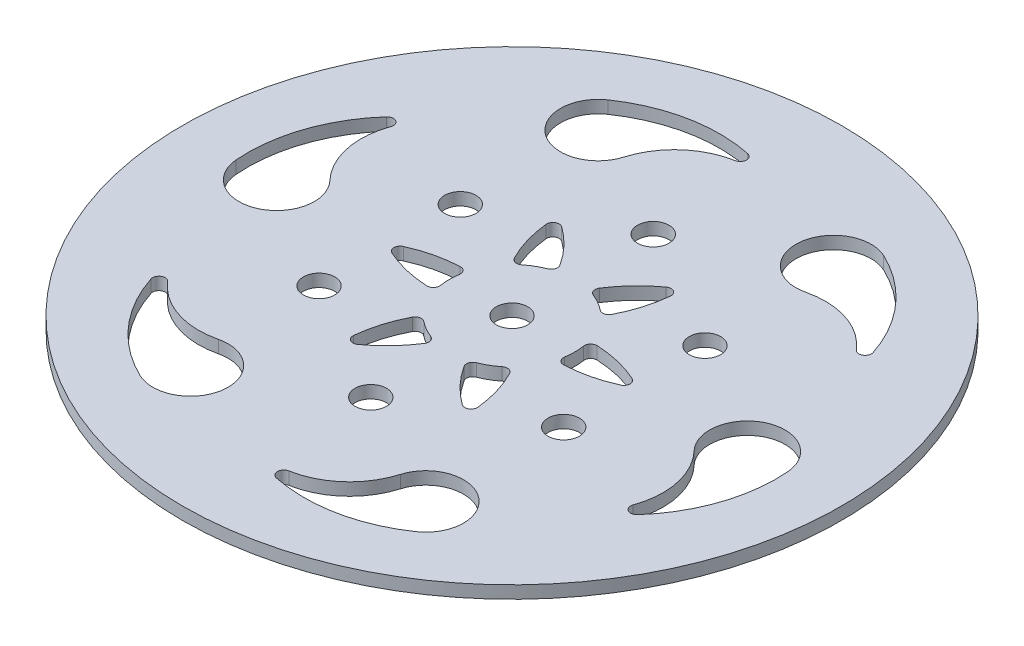
SolidWorks part; units mm, degrees
material "Thornel Mat VMA"
ref_plane "前视基准面" through (0, 0, 0) normal (0, 0, 1) x (1, 0, 0)
ref_plane "上视基准面" through (0, 0, 0) normal (0, 1, 0) x (1, 0, 0)
ref_plane "右视基准面" through (0, 0, 0) normal (1, 0, 0) x (0, 0, -1)
sketch "草图1" plane through (0, 0, 0) normal (0, 1, 0) x (1, 0, 0)
  circle A0 centre (0, 0) radius 52.5
  circle A2 centre (0, 0) radius 2.5
  point P19 (0, 0)
  point P33 (0, 0)
  dimension "D1" = 105
  dimension "D3" = 5
extrude "凸台-拉伸1" add sketch "草图1" along normal blind 2
sketch "草图2" plane through (0, 2, 0) normal (0, 1, 0) x (1, 0, 0)
  circle A0 centre (0, 0) radius 22.5 construction
  circle A1 centre (0, 22.5) radius 2.5
  circle A2 centre (19.4856, 11.25) radius 2.5
  circle A3 centre (19.4856, -11.25) radius 2.5
  circle A4 centre (0, -22.5) radius 2.5
  circle A5 centre (-19.4856, -11.25) radius 2.5
  circle A6 centre (-19.4856, 11.25) radius 2.5
  point P18 (0, 0)
  dimension "D1" = 45
  dimension "D2" = 5
  dimension "D3" = 6
extrude "切除-拉伸1" cut sketch "草图2" against normal through all
sketch "草图3" plane through (0, 2, 0) normal (0, 1, 0) x (1, 0, 0)
  line L0 (0, 0) -> (-10, 17.3205) construction
  arc A0 (-22.1556, 37.4158) -> (-12.9963, 30.7744) centre (-18.75, 32.476) ccw
  circle A6 centre (0, 0) radius 37.5 construction
  arc A8 (-3.6225, 39.1802) -> (-12.9963, 30.7744) centre (-1.489, 27.3714) ccw
  arc A9 (-22.1556, 37.4158) -> (-3.5945, 41.1428) centre (-8.5332, 17.6565) cw
  arc A10 (-3.5945, 41.1428) -> (-3.6225, 39.1802) centre (-3.8003, 40.1642) cw
  arc A11 (21.3252, 37.8952) -> (20.1533, 26.6424) centre (18.75, 32.476) ccw
  arc A12 (21.3252, 37.8952) -> (33.8335, 23.6843) centre (11.0244, 16.2182) cw
  arc A13 (32.1198, 22.7272) -> (20.1533, 26.6424) centre (22.9598, 14.9752) ccw
  arc A14 (33.8335, 23.6843) -> (32.1198, 22.7272) centre (32.8831, 23.3733) cw
  arc A15 (43.4808, 0.4794) -> (33.1496, -4.1321) centre (37.5, 0) ccw
  arc A16 (43.4808, 0.4794) -> (37.428, -17.4585) centre (19.5576, -1.4383) cw
  arc A17 (35.7423, -16.4529) -> (33.1496, -4.1321) centre (24.4488, -12.3962) ccw
  arc A18 (37.428, -17.4585) -> (35.7423, -16.4529) centre (36.6834, -16.791) cw
  arc A19 (22.1556, -37.4158) -> (12.9963, -30.7744) centre (18.75, -32.476) ccw
  arc A20 (22.1556, -37.4158) -> (3.5945, -41.1428) centre (8.5332, -17.6565) cw
  arc A21 (3.6225, -39.1802) -> (12.9963, -30.7744) centre (1.489, -27.3714) ccw
  arc A22 (3.5945, -41.1428) -> (3.6225, -39.1802) centre (3.8003, -40.1642) cw
  arc A23 (-21.3252, -37.8952) -> (-20.1533, -26.6424) centre (-18.75, -32.476) ccw
  arc A24 (-21.3252, -37.8952) -> (-33.8335, -23.6843) centre (-11.0244, -16.2182) cw
  arc A25 (-32.1198, -22.7272) -> (-20.1533, -26.6424) centre (-22.9598, -14.9752) ccw
  arc A26 (-33.8335, -23.6843) -> (-32.1198, -22.7272) centre (-32.8831, -23.3733) cw
  arc A27 (-43.4808, -0.4794) -> (-33.1496, 4.1321) centre (-37.5, 0) ccw
  arc A28 (-43.4808, -0.4794) -> (-37.428, 17.4585) centre (-19.5576, 1.4383) cw
  arc A29 (-35.7423, 16.4529) -> (-33.1496, 4.1321) centre (-24.4488, 12.3962) ccw
  arc A30 (-37.428, 17.4585) -> (-35.7423, 16.4529) centre (-36.6834, 16.791) cw
  arc A31 (-2.5, 9.6825) -> (-7.1353, 7.0063) centre (0, 0) ccw
  arc A32 (-7.1353, 7.0063) -> (-10, 17.3205) centre (10, 17.3205) cw
  circle A33 centre (0, 0) radius 20 construction
  arc A34 (-2.5, 9.6825) -> (-10, 17.3205) centre (-20, 0) ccw
  arc A35 (2.5, 9.6825) -> (10, 17.3205) centre (20, 0) cw
  arc A36 (7.1353, 7.0063) -> (10, 17.3205) centre (-10, 17.3205) ccw
  arc A37 (7.1353, 7.0063) -> (2.5, 9.6825) centre (0, 0) ccw
  arc A38 (9.6353, 2.6762) -> (20, 0) centre (10, -17.3205) cw
  arc A39 (9.6353, -2.6762) -> (20, 0) centre (10, 17.3205) ccw
  arc A40 (9.6353, -2.6762) -> (9.6353, 2.6762) centre (0, 0) ccw
  arc A41 (7.1353, -7.0063) -> (10, -17.3205) centre (-10, -17.3205) cw
  arc A42 (2.5, -9.6825) -> (10, -17.3205) centre (20, 0) ccw
  arc A43 (2.5, -9.6825) -> (7.1353, -7.0063) centre (0, 0) ccw
  arc A44 (-2.5, -9.6825) -> (-10, -17.3205) centre (-20, 0) cw
  arc A45 (-7.1353, -7.0063) -> (-10, -17.3205) centre (10, -17.3205) ccw
  arc A46 (-7.1353, -7.0063) -> (-2.5, -9.6825) centre (0, 0) ccw
  arc A47 (-9.6353, -2.6762) -> (-20, 0) centre (-10, 17.3205) cw
  arc A48 (-9.6353, 2.6762) -> (-20, 0) centre (-10, -17.3205) ccw
  arc A49 (-9.6353, 2.6762) -> (-9.6353, -2.6762) centre (0, 0) ccw
  point P22 (5.5553, 37.0862)
  dimension "D1" = 6
  dimension "D3" = 75
  dimension "D4" = 12
  dimension "D5" = 24
  dimension "D6" = 1
  dimension "D7" = 40
  dimension "D8" = 10
  dimension "D9" = 20
  dimension "D10" = 5
  dimension "D2" = 6
extrude "切除-拉伸2" cut sketch "草图3" against normal through all
fillet "圆角1" radius 1 18 edges at (-20, 1, 0) (-9.6353, 1, -2.6762) (-9.6353, 1, 2.6762) (-10, 1, 17.3205) (-7.1353, 1, 7.0063) (-2.5, 1, 9.6825) (10, 1, 17.3205) (2.5, 1, 9.6825) (7.1353, 1, 7.0063) (10, 1, -17.3205) (7.1353, 1, -7.0063) (2.5, 1, -9.6825) (-2.5, 1, -9.6825) (-10, 1, -17.3205) (20, 1, 0) (9.6353, 1, 2.6762) (9.6353, 1, -2.6762) (-7.1353, 1, -7.0063)
